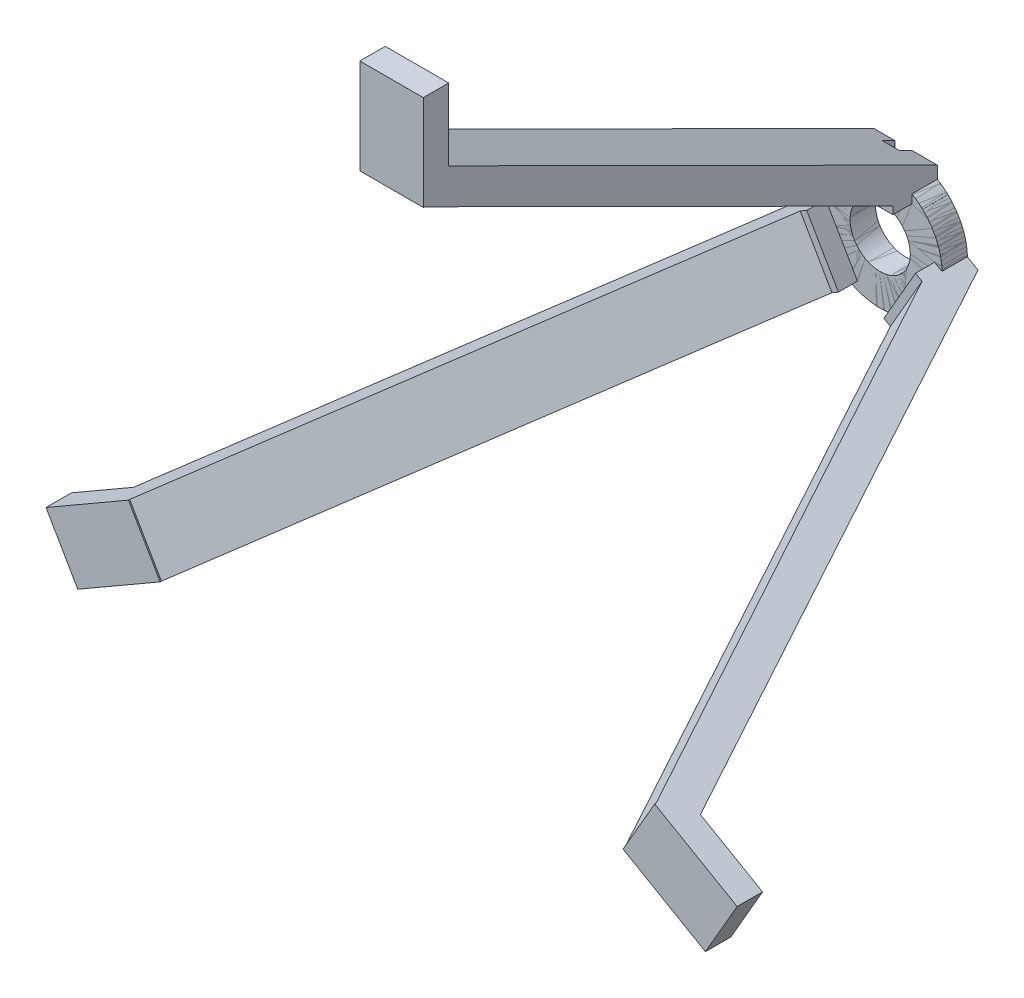
SolidWorks part; units mm, degrees
ref_plane "Front Plane" through (0, 0, 0) normal (0, 0, 1) x (1, 0, 0)
ref_plane "Top Plane" through (0, 0, 0) normal (0, 1, 0) x (1, 0, 0)
ref_plane "Right Plane" through (0, 0, 0) normal (1, 0, 0) x (0, 0, -1)
sketch "Sketch1" plane through (0, 0, 0) normal (0, 0, 1) x (1, 0, 0)
  line L0 (-6.6908, 7.0919) -> (6.6908, 7.0919)
  circle A0 centre (0, 0) radius 4.75
  circle A1 centre (0, 0) radius 9.75
  dimension "D1" = 9.5
  dimension "D2" = 19.5
extrude "Boss-Extrude1" add sketch "Sketch1" along normal blind 4 contours L0 A1 A0
sketch "Sketch2" plane through (0, 0, 4) normal (0, 0, 1) x (1, 0, 0)
  line L0 (0, 0) -> (0, 13.0507) construction
  line L1 (-5, 7.0173) -> (5, 7.0173)
  line L2 (-5, 7.0173) -> (-5, 10.287)
  line L3 (-5, 10.287) -> (5, 10.287)
  line L4 (5, 7.0173) -> (5, 10.287)
  dimension "D1" = 10
  dimension "D2" = 5
extrude "Boss-Extrude3" add sketch "Sketch2" along normal blind 3 and the other way blind 2
ref_plane "Plane2" through (0, 0, 81) normal (0, 0, 1) x (1, 0, 0)
sketch "Sketch6" plane through (0, 0, 81) normal (0, 0, 1) x (1, 0, 0)
  line L0 (0, 0) -> (0, 77.9527) construction
  line L1 (-5, 60) -> (5, 60)
  line L2 (-5, 60) -> (-5, 45)
  line L3 (-5, 45) -> (5, 45)
  line L4 (5, 60) -> (5, 45)
  line L5 (0, 0) -> (35.0232, 0) construction
  line L6 (0, 0) -> (-42.3784, 0) construction
  dimension "D1" = 45
  dimension "D2" = 15
  dimension "D3" = 5
  dimension "D4" = 10
extrude "Boss-Extrude4" add sketch "Sketch6" against normal blind 4 separate body
ref_plane "Plane3" through (-5, 0, 0) normal (-1, 0, 0) x (0, 0, 1)
sketch "Sketch7" plane through (-5, 0, 0) normal (-1, 0, 0) x (0, 0, 1)
  line L0 (-0.0027, 10.2925) -> (77, 48.6912)
  line L2 (80.802, 45) -> (7, 8.1973)
  line L4 (77, 45) -> (81, 45) construction
  line L5 (77, 60) -> (77, 45) construction
  line L6 (7, 10.287) -> (7, 7.0173) construction
  line L7 (-0.0027, 10.2925) -> (0, 7.0919)
  line L8 (0, 7.0919) -> (7, 7.0173)
  line L9 (7, 8.1973) -> (7, 7.0173)
  line L10 (77, 48.6912) -> (80.802, 45)
  dimension "D1" = 5
extrude "Boss-Extrude5" add sketch "Sketch7" against normal blind 10
pattern_circular "CirPattern2" count 3 over 360 about axis through (0, 0, 0) along (0, 0, 1) of bodies 106
sketch "Sketch8" plane through (0, 0, 0) normal (0, 0, -1) x (-1, 0, 0)
  line L1 (-1.0157, 6.9457) -> (1.6579, 6.9457)
  line L2 (-1.0157, 6.9457) -> (-1.0157, 11.6028)
  line L3 (-1.0157, 11.6028) -> (1.6579, 11.6028)
  line L4 (1.6579, 6.9457) -> (1.6579, 11.6028)
extrude "Cut-Extrude2" cut sketch "Sketch8" against normal blind 2 and the other way blind 2
sketch "Sketch9" plane through (0, 0, 2) normal (0, 0, -1) x (-1, 0, 0)
  line L0 (0, 0) -> (0.5997, 19.593) construction
